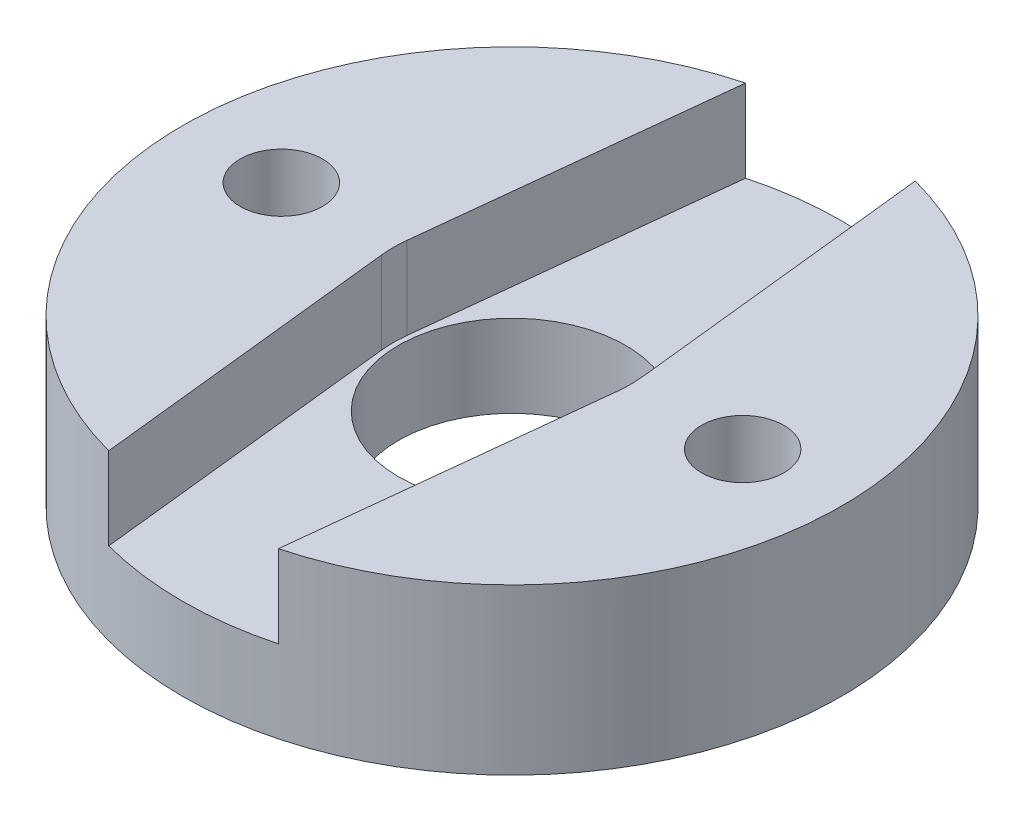
SolidWorks part; units mm, degrees
material "6061 Alloy"
ref_plane "Front Plane" through (0, 0, 0) normal (0, 0, 1) x (1, 0, 0)
ref_plane "Top Plane" through (0, 0, 0) normal (0, 1, 0) x (1, 0, 0)
ref_plane "Right Plane" through (0, 0, 0) normal (1, 0, 0) x (0, 0, -1)
sketch "Sketch1" plane through (0, 0, 0) normal (0, 1, 0) x (1, 0, 0)
  circle A0 centre (0, 0) radius 10
  dimension "D1" = 20
extrude "Boss-Extrude1" add sketch "Sketch1" along normal blind 5
ref_axis "Axis1" through (0, 5, 0) along (0, -1, 0)
hole_wizard "Tap Drill for M3x0.5 Tap1" positions "Sketch2" profile "Sketch3" hole size "M3x0.5" standard "ANSI Metric"
sketch "Sketch2" plane through (0, 5, 0) normal (0, 1, 0) x (1, 0, 0)
  point P0 (7, 0)
  dimension "D1" = 7
sketch "Sketch3" plane through (7, 5, 0) normal (1, 0, 0) x (0, 0, 1)
  line L0 (0, 0) -> (0, 38.1)
  line L1 (0, 38.1) -> (1.25, 38.1)
  line L2 (1.25, 38.1) -> (1.25, 0)
  line L5 (1.25, 0) -> (0, 0)
  line L10 (0, 38.1) -> (-1.25, 38.1) construction
  line L11 (0, -6.35) -> (0, 107.95) construction
  dimension "Hole Dia." = 2.5
  dimension "Hole Depth" = 38.1
  dimension "Drill Angle" = 180
pattern_circular "CirPattern1" count 4 over 360 about axis through (0, 5, 0) along (0, -1, 0) skipping 1, 3 of "Tap Drill for M3x0.5 Tap1"
hole_wizard "#14 (0.182) Diameter Hole1" positions "Sketch7" profile "Sketch5" hole size "#14" standard "ANSI Inch" end condition through all
sketch "Sketch7" plane through (0, 5, 0) normal (0, 1, 0) x (1, 0, 0)
  point P0 (0, 0)
sketch "Sketch5" plane through (0, 5, 0) normal (1, 0, 0) x (0, 0, 1)
  line L0 (0, 0) -> (0, 5)
  line L1 (0, 5) -> (3.45, 5)
  line L2 (3.45, 5) -> (3.45, 0)
  line L5 (3.45, 0) -> (0, 0)
  line L11 (0, -6.35) -> (0, 107.95) construction
  dimension "Thru Hole Dia." = 6.9
  dimension "Thru Hole Depth" = 5
sketch "Sketch10" plane through (0, 5, 0) normal (0, 1, 0) x (1, 0, 0)
  line L4 (-3.579, 0.3879) -> (-2.0579, 14.423)
  line L5 (3.579, 0.3879) -> (2.0579, 14.423)
  line L6 (3.579, -0.3879) -> (2.0579, -14.423)
  line L7 (-3.579, -0.3879) -> (-2.0579, -14.423)
  arc A4 (2.0579, 14.423) -> (-2.0579, 14.423) centre (0, 14.2) ccw
  arc A5 (3.579, -0.3879) -> (3.579, 0.3879) centre (0, 0) ccw
  arc A6 (-2.0579, -14.423) -> (2.0579, -14.423) centre (0, -14.2) ccw
  arc A7 (-3.579, 0.3879) -> (-3.579, -0.3879) centre (0, 0) ccw
  point P15 (0, 0)
extrude "Cut-Extrude3" cut sketch "Sketch10" against normal blind 2.5 contours L6 A6 L7 A7 L4 A4 L5 A5
